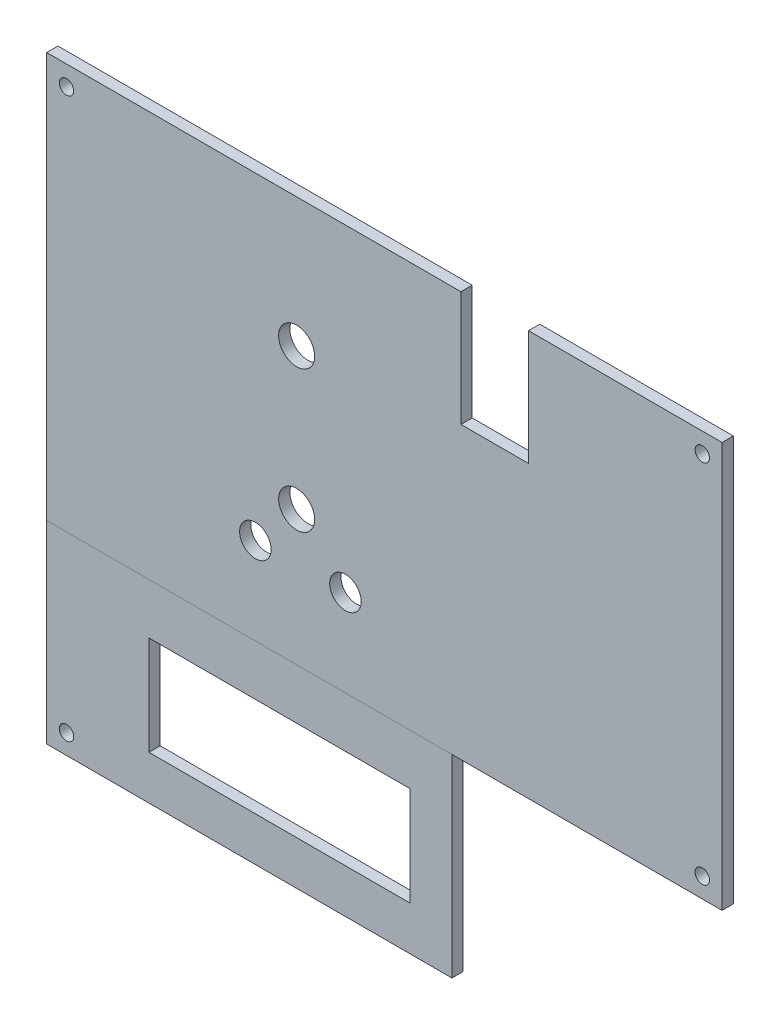
SolidWorks part; units mm, degrees
ref_plane "Front Plane" through (0, 0, 0) normal (0, 0, 1) x (1, 0, 0)
ref_plane "Top Plane" through (0, 0, 0) normal (0, 1, 0) x (1, 0, 0)
ref_plane "Right Plane" through (0, 0, 0) normal (1, 0, 0) x (0, 0, -1)
sketch "Model" plane through (0, 0, 0) normal (0, 0, 1) x (1, 0, 0)
  line L0 (124.1425, 93.5482) -> (108.3945, 93.5482)
  line L1 (124.1425, 74.9046) -> (124.1425, 93.5482)
  line L2 (108.3945, 74.9046) -> (124.1425, 74.9046)
  line L3 (108.3945, 93.5482) -> (108.3945, 74.9046)
  line L4 (169.8625, 95.25) -> (0, 95.25)
  line L5 (169.8625, 0) -> (169.8625, 95.25)
  line L6 (0, 0) -> (169.8625, 0)
  line L7 (0, 95.25) -> (0, 0)
  circle A0 centre (48.6791, 15.24) radius 2.9527
  circle A1 centre (74.0791, 15.24) radius 2.9528
  circle A2 centre (60.325, 79.629) radius 4.4704
  circle A3 centre (60.325, 39.751) radius 4.4704
  circle A4 centre (9.8107, 85.0836) radius 2.9528
  circle A5 centre (160.0517, 85.0836) radius 2.9527
  circle A6 centre (160.0517, 9.9631) radius 2.9528
  circle A7 centre (9.8107, 9.9631) radius 2.9527
  text T0 "SOLIDWORKS Educational Product." font "TXT" height 4.8336
  text T1 "For Instructional Use Only." font "TXT" height 4.8336
sketch "Sketch2" plane through (0, 0, 0) normal (0, 0, 1) x (1, 0, 0)
  line L9 (-10.1855, 105.0036) -> (180.3145, 105.0036)
  line L10 (-10.1855, 105.0036) -> (-10.1855, -9.2964)
  line L11 (-10.1855, -9.2964) -> (180.3145, -9.2964)
  line L12 (180.3145, 105.0036) -> (180.3145, -9.2964)
  line L13 (125.7045, 105.0036) -> (106.6545, 105.0036)
  line L14 (125.7045, 105.0036) -> (125.7045, 72.5729)
  line L15 (125.7045, 72.5729) -> (106.6545, 72.5729)
  line L16 (106.6545, 105.0036) -> (106.6545, 72.5729)
  circle A16 centre (60.325, 68.58) radius 5.08
  circle A17 centre (60.325, 28.702) radius 5.08
  circle A18 centre (48.6791, 15.24) radius 4.445
  circle A19 centre (74.0791, 15.24) radius 4.445
  point P12 (0, 0)
  point P13 (0, 0)
  point P14 (0, 0)
  dimension "D6" = 10.16
  dimension "D7" = 10.16
  dimension "D8" = 8.89
  dimension "D1" = 114.3
  dimension "D2" = 190.5
  dimension "D3" = 19.05
  dimension "D4" = 54.61
  dimension "D5" = 39.878
  dimension "D10" = 13.462
extrude "Boss-Extrude1" add sketch "Sketch2" along normal blind 3.175 contours L16 L9 L10 L11 L12 L14 L15 A19 A18 A17 A16
sketch "Sketch3" plane through (0, 0, 3.175) normal (0, 0, 1) x (1, 0, 0)
  line L1 (-10.1855, -9.2964) -> (104.1145, -9.2964)
  line L2 (-10.1855, -9.2964) -> (-10.1855, -63.9064)
  line L3 (-10.1855, -63.9064) -> (104.1145, -63.9064)
  line L4 (104.1145, -9.2964) -> (104.1145, -63.9064)
  dimension "D1" = 54.61
  dimension "D2" = 114.3
extrude "Boss-Extrude2" add sketch "Sketch3" against normal blind 3.175 separate body
sketch "Sketch4" plane through (0, 0, 3.175) normal (0, 0, 1) x (1, 0, 0)
  line L1 (18.6412, -23.5699) -> (92.3012, -23.5699)
  line L2 (18.6412, -23.5699) -> (18.6412, -51.5099)
  line L3 (18.6412, -51.5099) -> (92.3012, -51.5099)
  line L4 (92.3012, -23.5699) -> (92.3012, -51.5099)
  dimension "D3" = 73.66
  dimension "D4" = 27.94
extrude "Cut-Extrude1" cut sketch "Sketch4" against normal blind 3.175
sketch "Sketch6" plane through (0, 0, 3.175) normal (0, 0, 1) x (1, 0, 0)
  line L0 (-10.1855, 105.0036) -> (-10.1855, -9.2964) construction
  line L1 (-10.1855, 105.0036) -> (106.6545, 105.0036) construction
  line L2 (180.3145, 105.0036) -> (180.3145, -9.2964) construction
  line L3 (-10.1855, -9.2964) -> (180.3145, -9.2964) construction
  line L4 (-10.1855, -63.9064) -> (104.1145, -63.9064) construction
  circle A0 centre (-4.5975, 99.4156) radius 2.032
  circle A1 centre (174.7265, 99.4156) radius 2.032
  circle A2 centre (174.7265, -3.7084) radius 2.032
  circle A3 centre (-4.5975, -58.3184) radius 2.032
  dimension "D1" = 4.064
  dimension "D2" = 5.588
  dimension "D3" = 5.588
  dimension "D4" = 5.588
  dimension "D5" = 5.588
  dimension "D6" = 5.588
extrude "Cut-Extrude2" cut sketch "Sketch6" against normal through all
